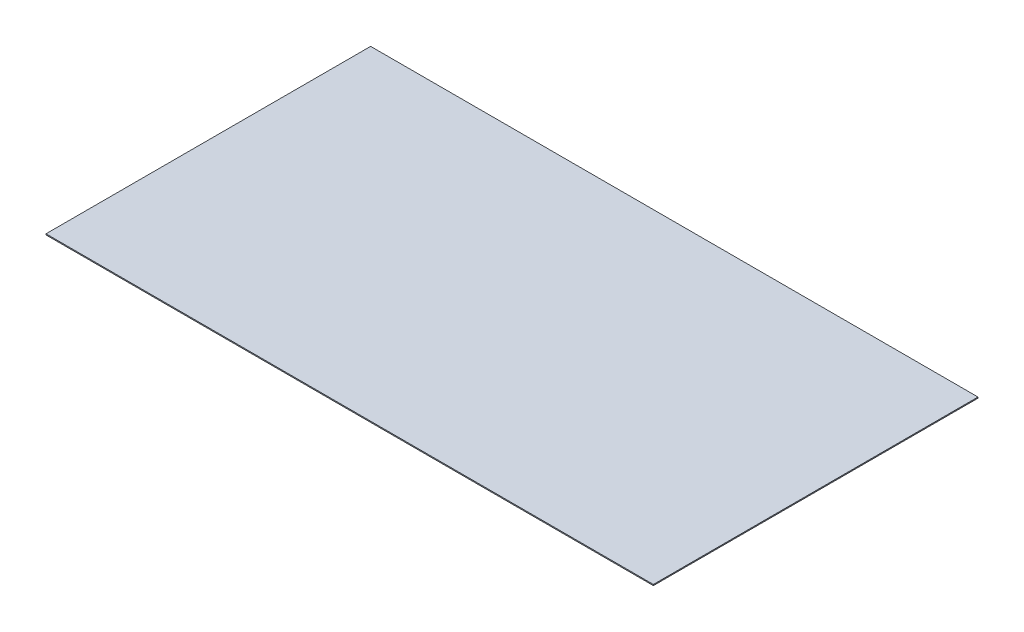
SolidWorks part; units mm, degrees
material "6061 Alloy"
ref_plane "Front" through (0, 0, 0) normal (0, 0, 1) x (1, 0, 0)
ref_plane "Top" through (0, 0, 0) normal (0, 1, 0) x (1, 0, 0)
ref_plane "Right" through (0, 0, 0) normal (1, 0, 0) x (0, 0, -1)
sketch "Sketch2" plane through (0, 0, 0) normal (0, 1, 0) x (1, 0, 0)
  line L1 (-290, -155) -> (290, -155)
  line L2 (-290, -155) -> (-290, 155)
  line L3 (-290, 155) -> (290, 155)
  line L4 (290, -155) -> (290, 155)
  line L5 (-290, -155) -> (290, 155) construction
  line L6 (-290, 155) -> (290, -155) construction
  point P0 (0, 0)
  dimension "D1" = 580
  dimension "D2" = 310
extrude "Boss-Extrude3" add sketch "Sketch2" along normal blind 1
